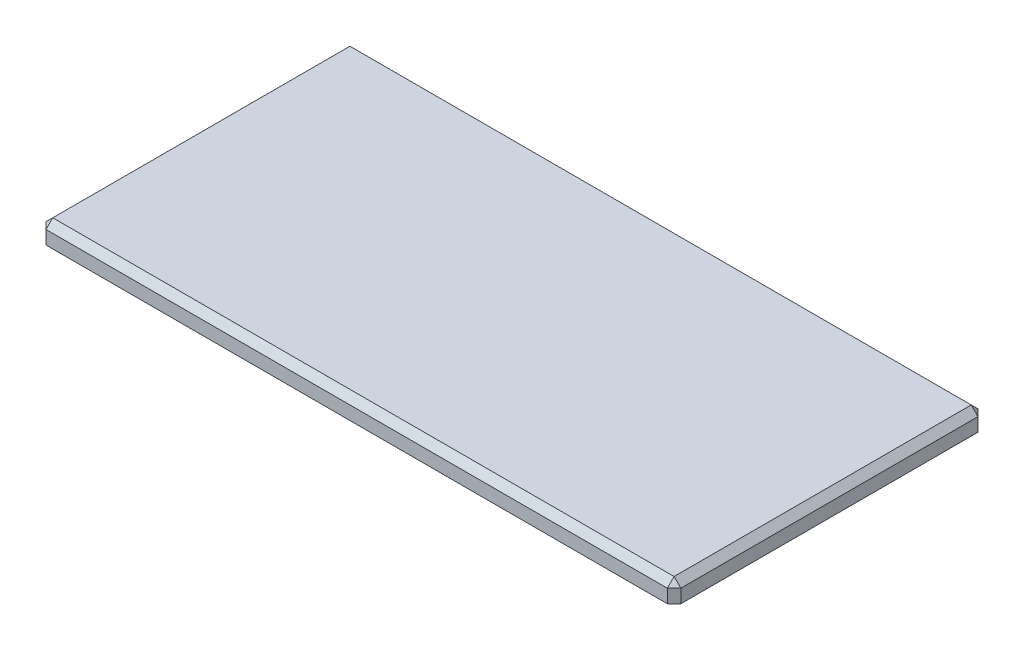
SolidWorks part; units mm, degrees
ref_plane "Front Plane" through (0, 0, 0) normal (0, 0, 1) x (1, 0, 0)
ref_plane "Top Plane" through (0, 0, 0) normal (0, 1, 0) x (1, 0, 0)
ref_plane "Right Plane" through (0, 0, 0) normal (1, 0, 0) x (0, 0, -1)
sketch "Sketch1" plane through (0, 0, 0) normal (0, 1, 0) x (1, 0, 0)
  line L1 (-32.9028, 13.8319) -> (14.0972, 13.8319)
  line L2 (-32.9028, 13.8319) -> (-32.9028, -9.1681)
  line L3 (-32.9028, -9.1681) -> (14.0972, -9.1681)
  line L4 (14.0972, 13.8319) -> (14.0972, -9.1681)
  dimension "D1" = 23
  dimension "D2" = 47
extrude "Boss-Extrude1" add sketch "Sketch1" along normal blind 1.5
chamfer "Chamfer1" distance 0.5 angle 45 8 edges at (14.0972, 0.75, 9.1681) (14.0972, 0.75, -13.8319) (-32.9028, 0.75, -13.8319) (-32.9028, 0.75, 9.1681) (-32.9028, 1.5, -2.3319) (-9.4028, 1.5, -13.8319) (14.0972, 1.5, -2.3319) (-9.4028, 1.5, 9.1681)
